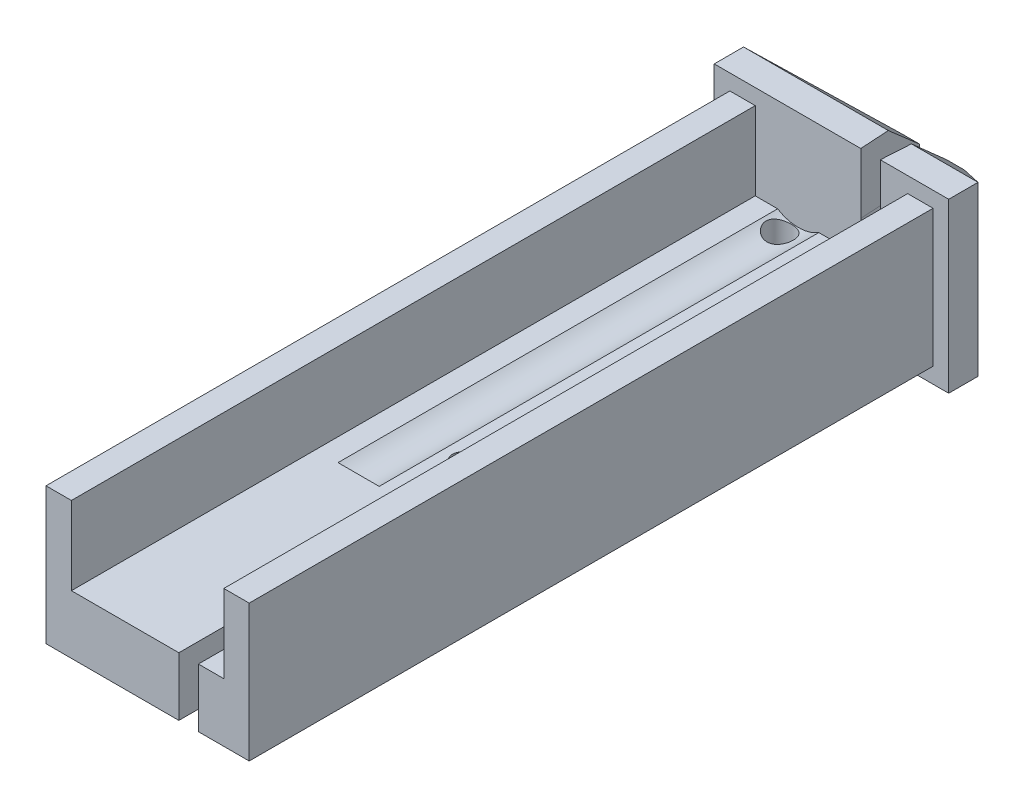
SolidWorks part; units mm, degrees
material "Custom Plastic"
ref_plane "Front Plane" through (0, 0, 0) normal (0, 0, 1) x (1, 0, 0)
ref_plane "Top Plane" through (0, 0, 0) normal (0, 1, 0) x (1, 0, 0)
ref_plane "Right Plane" through (0, 0, 0) normal (1, 0, 0) x (0, 0, -1)
sketch "Sketch4" plane through (0, 0, 0) normal (0, 0, 1) x (1, 0, 0)
  line L1 (0, 0) -> (-8, 0)
  line L2 (0, 0) -> (0, 5)
  line L3 (0, 5) -> (-8, 5)
  line L4 (-8, 0) -> (-8, 5)
  dimension "D1" = 8
extrude "Extrude1" add sketch "Sketch4" along normal blind 19.1
sketch "Sketch6" plane through (0, 0, 0) normal (1, 0, 0) x (0, 0, -1)
  line L1 (-19.3069, 0.75) -> (-1.6, 0.75)
  line L2 (-19.3069, 0.75) -> (-19.3069, -0.9122)
  line L3 (-19.3069, -0.9122) -> (-1.6, -0.9122)
  line L4 (-1.6, 0.75) -> (-1.6, -0.9122)
  line L7 (-19.1, 0) -> (0, 0) construction
  line L8 (0, 0) -> (0, 5) construction
  dimension "D1" = 0.75
  dimension "D2" = 1.6
extrude "Cut-Extrude1" cut sketch "Sketch6" against normal blind 18.6
sketch "Sketch7" plane through (0, 0, 0) normal (1, 0, 0) x (0, 0, -1)
  line L0 (-19.1, 5) -> (0, 5) construction
  line L1 (-19.192, 5.5827) -> (-1.6, 5.5827)
  line L2 (-19.192, 5.5827) -> (-19.192, 4.25)
  line L3 (-19.192, 4.25) -> (-1.6, 4.25)
  line L4 (-1.6, 5.5827) -> (-1.6, 4.25)
  line L5 (0, 0) -> (0, 5) construction
  dimension "D1" = 0.75
  dimension "D2" = 1.6
extrude "Cut-Extrude2" cut sketch "Sketch7" against normal blind 18.6
sketch "Sketch8" plane through (0, 0.75, 0) normal (0, -1, 0) x (1, 0, 0)
  line L0 (-8, 1.6) -> (-8, 19.1) construction
  line L1 (-11.9007, 19.3657) -> (-6.6, 19.3657)
  line L2 (-11.9007, 19.3657) -> (-11.9007, 1.6)
  line L3 (-11.9007, 1.6) -> (-6.6, 1.6)
  line L4 (-6.6, 19.3657) -> (-6.6, 1.6)
  line L5 (0, 1.6) -> (0, 19.1) construction
  line L6 (-1.4, 19.3954) -> (1.5439, 19.3954)
  line L7 (-1.4, 19.3954) -> (-1.4, 1.6)
  line L8 (-1.4, 1.6) -> (1.5439, 1.6)
  line L9 (1.5439, 19.3954) -> (1.5439, 1.6)
  line L10 (-8, 0) -> (0, 0) construction
  dimension "D1" = 1.4
  dimension "D2" = 1.4
  dimension "D3" = 1.6
  dimension "D4" = 1.6
extrude "Cut-Extrude3" cut sketch "Sketch8" against normal blind 18.6
sketch "Sketch10" plane through (0, 4.25, 0) normal (0, 1, 0) x (1, 0, 0)
  line L0 (-6.6, -1.6) -> (-6.6, -19.1) construction
  line L1 (-2.05, -19.5905) -> (-5.95, -19.5905)
  line L2 (-2.05, -19.5905) -> (-2.05, -1.6)
  line L3 (-2.05, -1.6) -> (-5.95, -1.6)
  line L4 (-5.95, -19.5905) -> (-5.95, -1.6)
  line L5 (-1.4, -19.1) -> (-1.4, -1.6) construction
  line L6 (0, 0) -> (-8, 0) construction
  dimension "D1" = 0.65
  dimension "D2" = 0.65
  dimension "D3" = 1.6
extrude "Cut-Extrude4" cut sketch "Sketch10" against normal blind 2
sketch "Sketch11" plane through (0, 2.25, 0) normal (0, 1, 0) x (1, 0, 0)
  line L0 (-2.05, -19.1) -> (-5.95, -19.1) construction
  line L2 (-2.05, -1.6) -> (-2.05, -19.1) construction
  circle A0 centre (-3.85, -11.2) radius 0.25
  dimension "D1" = 0.5
  dimension "D2" = 7.9
  dimension "D3" = 1.8
extrude "Cut-Extrude5" cut sketch "Sketch11" against normal blind 2
sketch "Sketch12" plane through (0, 2.25, 0) normal (0, 1, 0) x (1, 0, 0)
  line L0 (-5.95, -1.6) -> (-5.95, -19.1) construction
  line L2 (-3.2, -19.0996) -> (-3.2, -11.0996)
  line L4 (-2.7, -19.0996) -> (-2.7, -11.0996)
  arc A0 (-3.2, -11.0996) -> (-2.7, -11.0996) centre (-2.95, -11.0996) cw
  arc A1 (-2.7, -19.0996) -> (-3.2, -19.0996) centre (-2.95, -19.0996) cw
  dimension "D3" = 0.25
  dimension "D1" = 8
  dimension "D2" = 2.75
extrude "Cut-Extrude6" cut sketch "Sketch12" against normal blind 2
sketch "Sketch14" plane through (0, 2.25, 0) normal (0, 1, 0) x (1, 0, 0)
  line L1 (-5.95, -1.6) -> (-5.95, -19.1) construction
  line L6 (-8, -1.6) -> (0, -1.6) construction
  circle A0 centre (-4.95, -1.975) radius 0.35
  dimension "D1" = 1
  dimension "D6" = 0.375
extrude "Cut-Extrude8" cut sketch "Sketch14" against normal blind 2
sketch "Sketch28" plane through (0, 0, 1.6) normal (0, 0, 1) x (1, 0, 0)
  line L0 (-3.25, 3.1) -> (-3.25, 5)
  line L1 (-5.95, 4.25) -> (-5.95, 2.25) construction
  line L2 (-2.75, 3.1) -> (-2.75, 5)
  line L3 (-3.25, 5) -> (-2.75, 5)
  line L4 (-8, 5) -> (0, 5) construction
  arc A0 (-3.25, 3.1) -> (-2.75, 3.1) centre (-3, 3.1) ccw
  dimension "D1" = 0.5
  dimension "D2" = 0.85
  dimension "D3" = 2.95
extrude "Cut-Extrude16" cut sketch "Sketch28" against normal through all draft 3.5 draft outward yes
sketch "Sketch29" plane through (0, 0, 1.6) normal (0, 0, 1) x (1, 0, 0)
  line L0 (-6.6, 0.75) -> (-6.6, 4.25) construction
  line L1 (-7, 4.65) -> (-1, 4.65)
  line L2 (-7, 4.65) -> (-7, 0.35)
  line L3 (-7, 0.35) -> (-1, 0.35)
  line L4 (-1, 4.65) -> (-1, 0.35)
  line L5 (-1.4, 4.25) -> (-1.4, 0.75) construction
  line L6 (-1.4, 0.75) -> (-2.7, 0.75) construction
  line L7 (-6.6, 4.25) -> (-5.95, 4.25) construction
  line L9 (-8, 5) -> (0, 5)
  line L10 (-8, 5) -> (-8, 0)
  line L11 (-8, 0) -> (0, 0)
  line L12 (0, 5) -> (0, 0)
  dimension "D1" = 0.4
  dimension "D2" = 0.4
  dimension "D3" = 0.4
  dimension "D4" = 0.4
extrude "Cut-Extrude19" cut sketch "Sketch29" against normal blind 2.5
sketch "Sketch18" plane through (0, 4.65, 0) normal (0, 1, 0) x (1, 0, 0)
  line L0 (-3.8, 0) -> (-7, -0.85)
  line L2 (-7, 0) -> (-7, -1.6) construction
  line L3 (-7, -0.85) -> (-7, 0)
  line L5 (-7, 0) -> (-3.8, 0)
  line L6 (-2.2, 0) -> (-1, 0)
  line L7 (-1, 0) -> (-1, -0.85)
  line L8 (-1, 0) -> (-1, -1.6) construction
  line L9 (-1, -0.85) -> (-2.2, 0)
  dimension "D1" = 3.2
  dimension "D2" = 0.75
  dimension "D3" = 1.2
extrude "Cut-Extrude20" cut sketch "Sketch18" against normal through all
sketch "Sketch30" plane through (-7, 0, 0) normal (-1, 0, 0) x (0, 0, 1)
  line L0 (0, 3.9) -> (0.85, 4.65)
  line L1 (0, 0.35) -> (0, 4.65) construction
  line L2 (0.85, 4.65) -> (0, 4.65)
  line L3 (0, 4.65) -> (0, 3.9)
  line L4 (0, 2.3) -> (0.85, 0.35)
  line L5 (0.85, 0.35) -> (0, 0.35)
  line L6 (0, 0.35) -> (0, 2.3)
  dimension "D1" = 1.95
  dimension "D4" = 0.75
extrude "Cut-Extrude21" cut sketch "Sketch30" against normal through all
sketch "Sketch19" plane through (0, 0, 1.6) normal (0, 0, 1) x (1, 0, 0)
  line L0 (-5.95, 4.25) -> (-5.95, 2.25) construction
  line L1 (-2.05, 2.25) -> (-5.95, 2.25) construction
  circle A1 centre (-4.85, 3.1) radius 1
  dimension "D4" = 2
  dimension "D1" = 1.1
  dimension "D6" = 0.85
extrude "Cut-Extrude11" cut sketch "Sketch19" along normal blind 11.25
